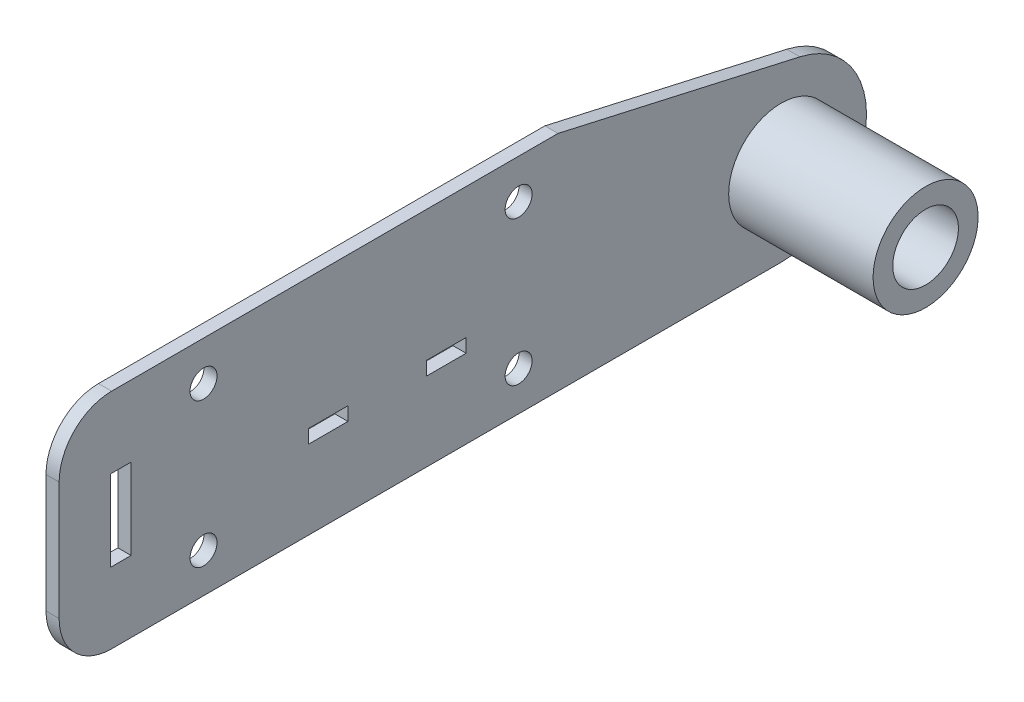
SolidWorks part; units mm, degrees
material "Plain Carbon Steel"
ref_plane "Front Plane" through (0, 0, 0) normal (0, 0, 1) x (1, 0, 0)
ref_plane "Top Plane" through (0, 0, 0) normal (0, 1, 0) x (1, 0, 0)
ref_plane "Right Plane" through (0, 0, 0) normal (1, 0, 0) x (0, 0, -1)
sketch "Sketch1" plane through (0, 0, 0) normal (1, 0, 0) x (0, 0, -1)
  line L0 (47.625, -26.9875) -> (101.6, -26.9875)
  line L1 (38.1, 17.4625) -> (-38.1, 17.4625)
  line L2 (38.1, 17.4625) -> (38.1, -17.4625)
  line L3 (38.1, -17.4625) -> (-38.1, -17.4625)
  line L4 (-38.1, 17.4625) -> (-38.1, -17.4625)
  line L5 (38.1, 17.4625) -> (-38.1, -17.4625) construction
  line L6 (38.1, -17.4625) -> (-38.1, 17.4625) construction
  line L7 (-47.625, 26.9875) -> (47.625, 26.9875)
  line L8 (-47.625, 26.9875) -> (-47.625, -26.9875)
  line L9 (-47.625, -26.9875) -> (47.625, -26.9875)
  line L10 (47.625, 26.9875) -> (47.625, -26.9875)
  line L11 (-47.625, 26.9875) -> (47.625, -26.9875) construction
  line L12 (-47.625, -26.9875) -> (47.625, 26.9875) construction
  line L13 (47.625, 26.9875) -> (106.1432, 13.7812)
  circle A0 centre (-38.1, 17.4625) radius 3.2639
  circle A1 centre (-38.1, -17.4625) radius 3.2639
  circle A2 centre (38.1, -17.4625) radius 3.2639
  circle A3 centre (38.1, 17.4625) radius 3.2639
  circle A4 centre (101.6, -6.35) radius 12.7
  circle A5 centre (101.6, -6.35) radius 20.6375
  point P0 (0, 0)
  point P13 (0, 0)
  dimension "D3" = 6.5278
  dimension "D4" = 25.4
  dimension "D1" = 76.2
  dimension "D2" = 34.925
  dimension "D5" = 63.5
  dimension "D6" = 6.35
  dimension "D8" = 9.525
  dimension "D9" = 9.525
extrude "Boss-Extrude1" add sketch "Sketch1" along normal blind 3.175 contours L10 L7 L8 L9 A3 L2 A2 L3 A1 L4 A0 L1 | A3 L1 A0 L4 A1 L3 A2 L2 | A5 L13 L10 L0 | A5 A4
sketch "Sketch2" plane through (0, 0, 0) normal (-1, 0, 0) x (0, 0, 1)
  circle A0 centre (-101.6, -6.35) radius 12.7 construction
  circle A1 centre (-101.6, -6.35) radius 12.7
  circle A2 centre (-101.6, -6.35) radius 7.9375
  dimension "D1" = 4.7625
extrude "Boss-Extrude2" add sketch "Sketch2" against normal blind 38.1
sketch "Sketch4" plane through (3.175, 0, 0) normal (1, 0, 0) x (0, 0, -1)
  line L0 (-47.625, -26.9875) -> (101.6, -26.9875) construction
  line L1 (-47.625, 26.9875) -> (-60.325, 26.9875)
  line L2 (-47.625, 26.9875) -> (-47.625, -26.9875)
  line L3 (-47.625, -26.9875) -> (-60.325, -26.9875)
  line L4 (-73.025, 14.2875) -> (-73.025, -14.2875)
  line L6 (-60.579, 9.779) -> (-55.626, 9.779)
  line L7 (-60.579, 9.779) -> (-60.579, -9.779)
  line L8 (-60.579, -9.779) -> (-55.626, -9.779)
  line L9 (-55.626, 9.779) -> (-55.626, -9.779)
  arc A0 (-60.325, 26.9875) -> (-73.025, 14.2875) centre (-60.325, 14.2875) ccw
  arc A1 (-60.325, -26.9875) -> (-73.025, -14.2875) centre (-60.325, -14.2875) cw
  point P13 (-73.025, 26.9875)
  dimension "D6" = 12.7
  dimension "D1" = 25.4
  dimension "D2" = 19.558
  dimension "D3" = 4.953
  dimension "D4" = 17.2085
  dimension "D5" = 8.001
extrude "Boss-Extrude3" add sketch "Sketch4" against normal up to surface (3.175 mm away) up to face at (0, -17.4625, -41.3639)
sketch "Sketch5" plane through (3.175, 0, 0) normal (1, 0, 0) x (0, 0, -1)
  line L1 (15.875, -4.6355) -> (25.4, -4.6355)
  line L2 (15.875, -4.6355) -> (15.875, -7.9375)
  line L3 (15.875, -7.9375) -> (25.4, -7.9375)
  line L4 (25.4, -4.6355) -> (25.4, -7.9375)
  line L5 (-12.7, -4.6355) -> (-3.175, -4.6355)
  line L6 (-12.7, -4.6355) -> (-12.7, -7.9375)
  line L7 (-12.7, -7.9375) -> (-3.175, -7.9375)
  line L8 (-3.175, -4.6355) -> (-3.175, -7.9375)
  circle A0 centre (101.6, -6.35) radius 12.7 construction
  circle A1 centre (101.6, -6.35) radius 12.7 construction
  dimension "D1" = 3.302
  dimension "D2" = 1.5875
  dimension "D3" = 9.525
  dimension "D4" = 76.2
  dimension "D5" = 9.525
  dimension "D6" = 19.05
  dimension "D7" = 3.302
extrude "Cut-Extrude1" cut sketch "Sketch5" against normal through all
